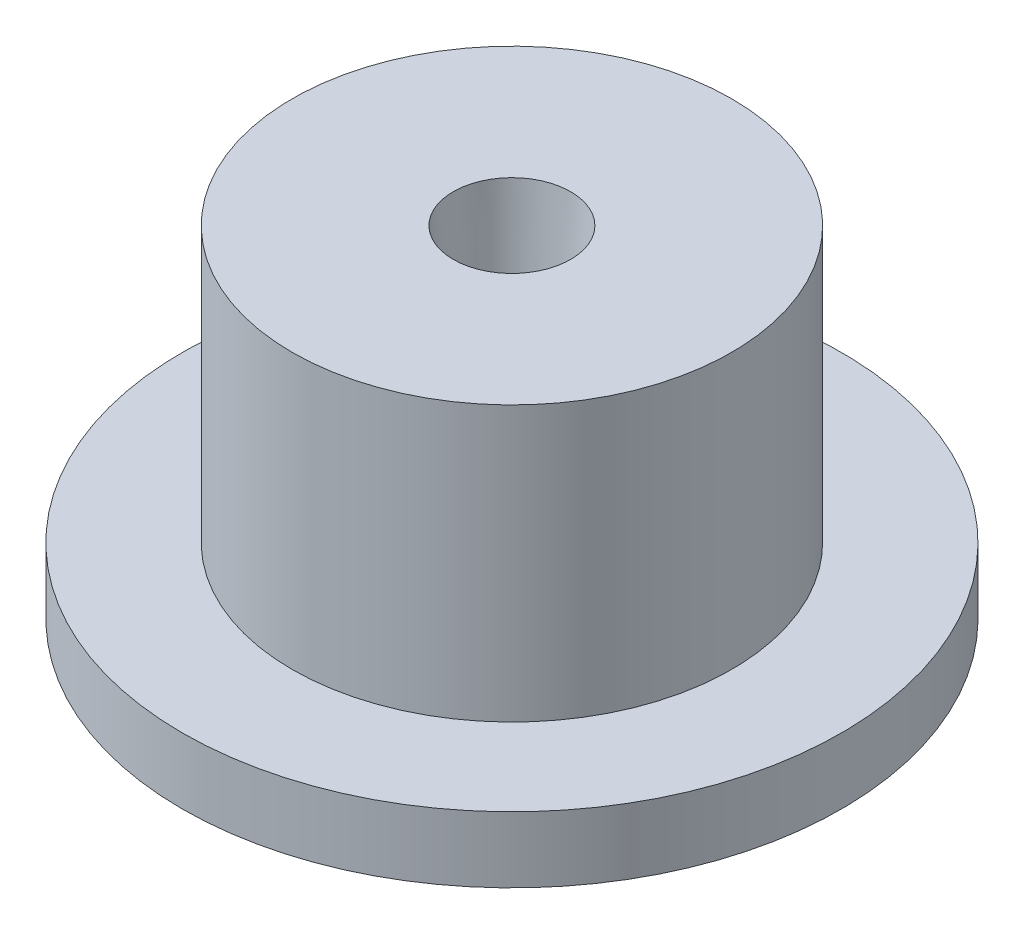
SolidWorks part; units mm, degrees
ref_plane "Front Plane" through (0, 0, 0) normal (0, 0, 1) x (1, 0, 0)
ref_plane "Top Plane" through (0, 0, 0) normal (0, 1, 0) x (1, 0, 0)
ref_plane "Right Plane" through (0, 0, 0) normal (1, 0, 0) x (0, 0, -1)
sketch "Sketch1" plane through (0, 0, 0) normal (0, 0, 1) x (1, 0, 0)
  line L0 (0, 20.6667) -> (0, -19.6232) construction
  line L1 (0.6404, 0) -> (6, 0)
  line L2 (6, 0) -> (6, 1.2)
  line L3 (6, 1.2) -> (4, 1.2)
  line L4 (4, 1.2) -> (4, 6.2)
  line L5 (4, 6.2) -> (1.0687, 6.2)
  line L7 (0.6404, 0) -> (1.0687, 6.2)
  dimension "D1" = 8
  dimension "D2" = 6.2
  dimension "D3" = 1.2
  dimension "D4" = 12
revolve "Revolve1" add sketch "Sketch1" angle 360 about L0
